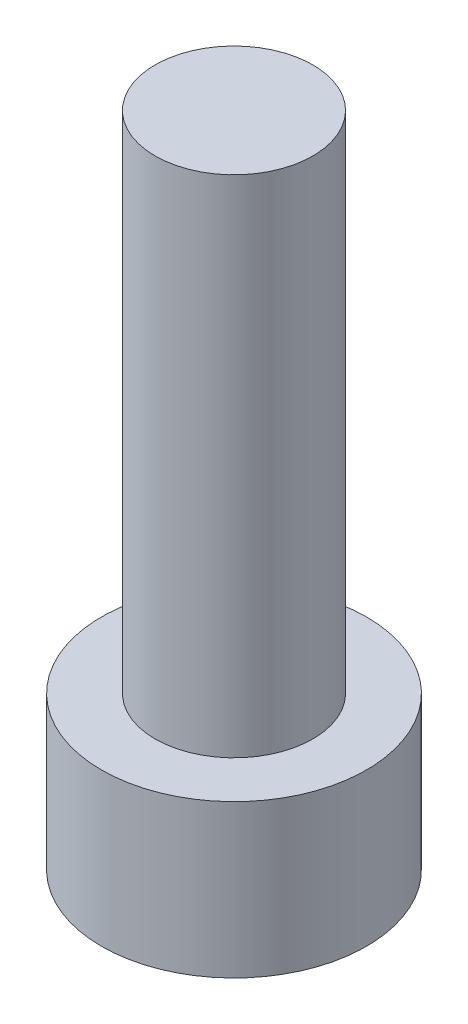
SolidWorks part; units mm, degrees
ref_plane "前视基准面" through (0, 0, 0) normal (0, 0, 1) x (1, 0, 0)
ref_plane "上视基准面" through (0, 0, 0) normal (0, 1, 0) x (1, 0, 0)
ref_plane "右视基准面" through (0, 0, 0) normal (1, 0, 0) x (0, 0, -1)
sketch "草图1" plane through (0, 0, 0) normal (0, 1, 0) x (1, 0, 0)
  circle A0 centre (0, 0) radius 4.2
extrude "凸台-拉伸1" add sketch "草图1" along normal blind 4.84
sketch "草图2" plane through (0, 4.84, 0) normal (0, 1, 0) x (1, 0, 0)
  circle A0 centre (0, 0) radius 2.5
extrude "凸台-拉伸2" add sketch "草图2" along normal blind 16
sketch "草图3" plane through (0, 0, 0) normal (0, -1, 0) x (1, 0, 0)
  line L1 (2.3, 0) -> (1.15, 1.9919)
  line L2 (1.15, 1.9919) -> (-1.15, 1.9919)
  line L3 (-1.15, 1.9919) -> (-2.3, 0)
  line L4 (-2.3, 0) -> (-1.15, -1.9919)
  line L5 (-1.15, -1.9919) -> (1.15, -1.9919)
  line L6 (1.15, -1.9919) -> (2.3, 0)
  circle A0 centre (0, 0) radius 1.9919 construction
extrude "切除-拉伸1" cut sketch "草图3" against normal blind 3.4
